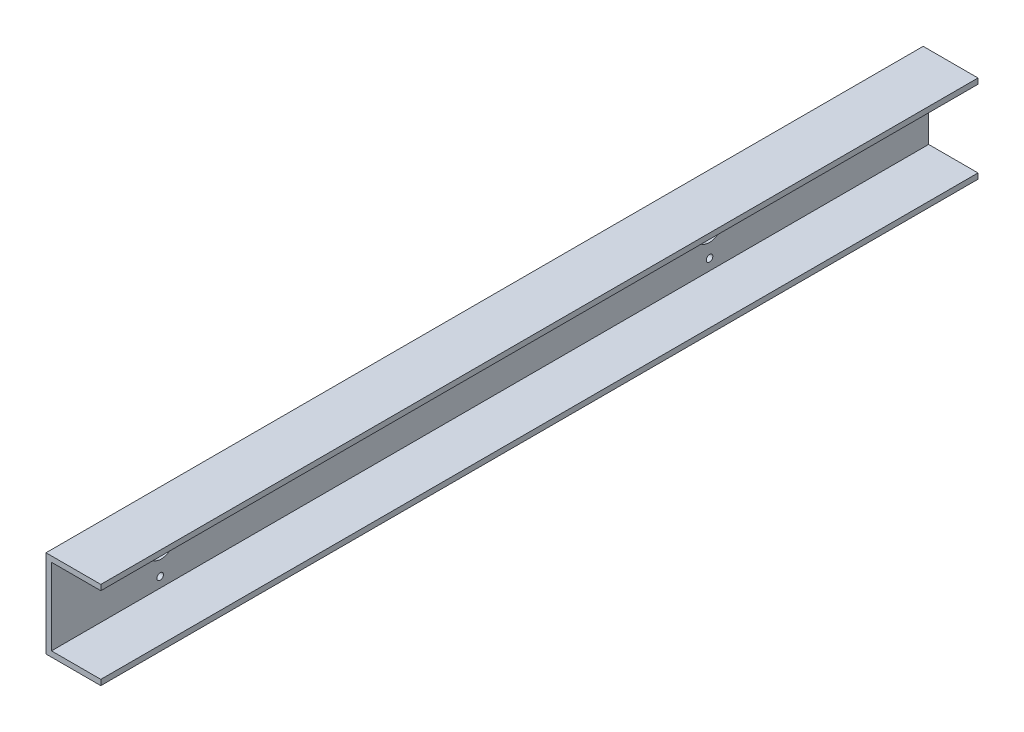
SolidWorks part; units mm, degrees
ref_plane "Front Plane" through (0, 0, 0) normal (0, 0, 1) x (1, 0, 0)
ref_plane "Top Plane" through (0, 0, 0) normal (0, 1, 0) x (1, 0, 0)
ref_plane "Right Plane" through (0, 0, 0) normal (1, 0, 0) x (0, 0, -1)
sketch "Sketch1" plane through (0, 0, 0) normal (0, 0, 1) x (1, 0, 0)
  line L0 (23.8333, 42.5) -> (-26.1667, 42.5)
  line L1 (-26.1667, 42.5) -> (-26.1667, -37.5)
  line L2 (-26.1667, -37.5) -> (23.8333, -37.5)
  line L3 (23.8333, -37.5) -> (23.8333, -32.5)
  line L4 (23.8333, -32.5) -> (-21.1667, -32.5)
  line L5 (-21.1667, -32.5) -> (-21.1667, 37.5)
  line L6 (-21.1667, 37.5) -> (23.8333, 37.5)
  line L7 (23.8333, 37.5) -> (23.8333, 42.5)
  dimension "D1" = 80
  dimension "D2" = 70
  dimension "D3" = 5
  dimension "D4" = 5
  dimension "D5" = 50
extrude "Boss-Extrude1" add sketch "Sketch1" along normal mid plane 800
sketch "Sketch2" plane through (-26.1667, 0, 0) normal (-1, 0, 0) x (0, 0, 1)
  line L0 (-400, 42.5) -> (-400, -37.5) construction
  line L1 (400, 42.5) -> (400, -37.5) construction
  line L2 (400, 42.5) -> (-400, 42.5) construction
  circle A0 centre (-200, 2.5) radius 12.5
  circle A1 centre (300, 2.5) radius 12.5
  dimension "D1" = 25
  dimension "D2" = 25
  dimension "D3" = 200
  dimension "D4" = 100
  dimension "D5" = 40
  dimension "D6" = 40
extrude "Cut-Extrude1" cut sketch "Sketch2" against normal through all both and the other way through all
sketch "Sketch4" plane through (-26.1667, 0, 0) normal (-1, 0, 0) x (0, 0, 1)
  circle A0 centre (-200.1583, 27.5) radius 3
  circle A1 centre (-200.1583, -22.5) radius 3
  circle A2 centre (-175, 3.3782) radius 3
  circle A3 centre (-224.9974, 2.8638) radius 3
  circle A4 centre (-200, 2.5) radius 12.5 construction
  dimension "D1" = 6
  dimension "D2" = 6
  dimension "D3" = 6
  dimension "D4" = 6
  dimension "D5" = 50
  dimension "D6" = 50
  dimension "D7" = 25
  dimension "D8" = 25
  dimension "D9" = 25
  dimension "D10" = 25
extrude "Cut-Extrude2" cut sketch "Sketch4" against normal through all both and the other way through all
sketch "Sketch6" plane through (-26.1667, 0, 0) normal (-1, 0, 0) x (0, 0, 1)
  circle A0 centre (299.206, 26.66) radius 3
  circle A1 centre (325.0137, 2.4946) radius 3
  circle A2 centre (300.8483, -23.313) radius 3
  circle A3 centre (275.0406, 0.8524) radius 3
  point P10 (300.0272, 1.6735)
  dimension "D2" = 6
  dimension "D1" = 4
extrude "Cut-Extrude3" cut sketch "Sketch6" against normal through all both and the other way through all
